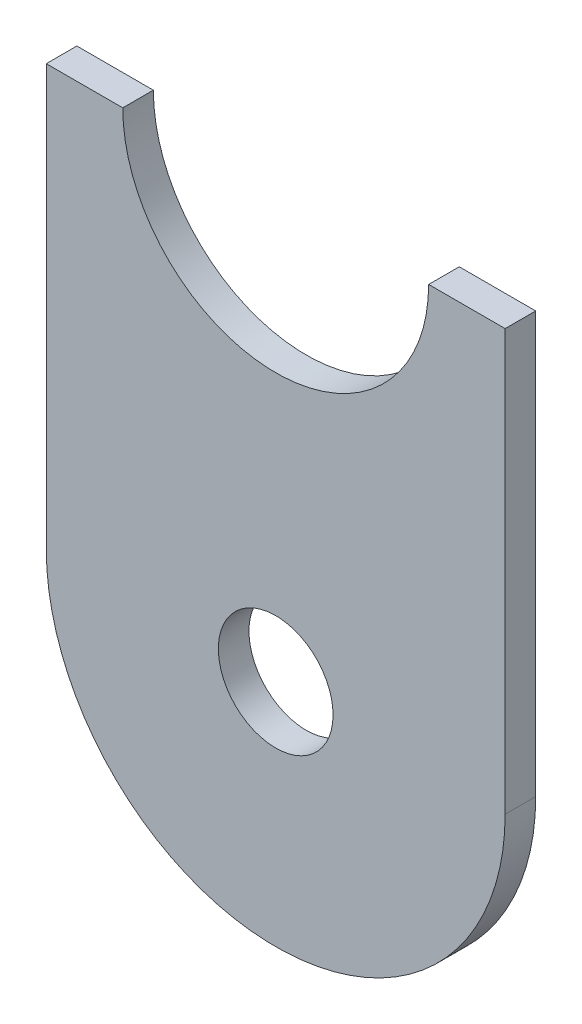
SolidWorks part; units mm, degrees
ref_plane "Front Plane" through (0, 0, 0) normal (0, 0, 1) x (1, 0, 0)
ref_plane "Top Plane" through (0, 0, 0) normal (0, 1, 0) x (1, 0, 0)
ref_plane "Right Plane" through (0, 0, 0) normal (1, 0, 0) x (0, 0, -1)
sketch "Sketch1" plane through (0, 0, 0) normal (0, 0, 1) x (1, 0, 0)
  line L1 (-19.05, -34.925) -> (19.05, -34.925)
  line L2 (-19.05, -34.925) -> (-19.05, 34.925)
  line L3 (-19.05, 34.925) -> (19.05, 34.925)
  line L4 (19.05, -34.925) -> (19.05, 34.925)
  line L5 (-19.05, -34.925) -> (19.05, 34.925) construction
  line L6 (-19.05, 34.925) -> (19.05, -34.925) construction
  circle A0 centre (0, 0) radius 19.05
  circle A1 centre (0, 0) radius 4.7625
  circle A2 centre (0, 34.925) radius 12.7
extrude "Boss-Extrude1" add sketch "Sketch1" along normal blind 2.54 contours A2 L2 A0 L4 | A0 A1
